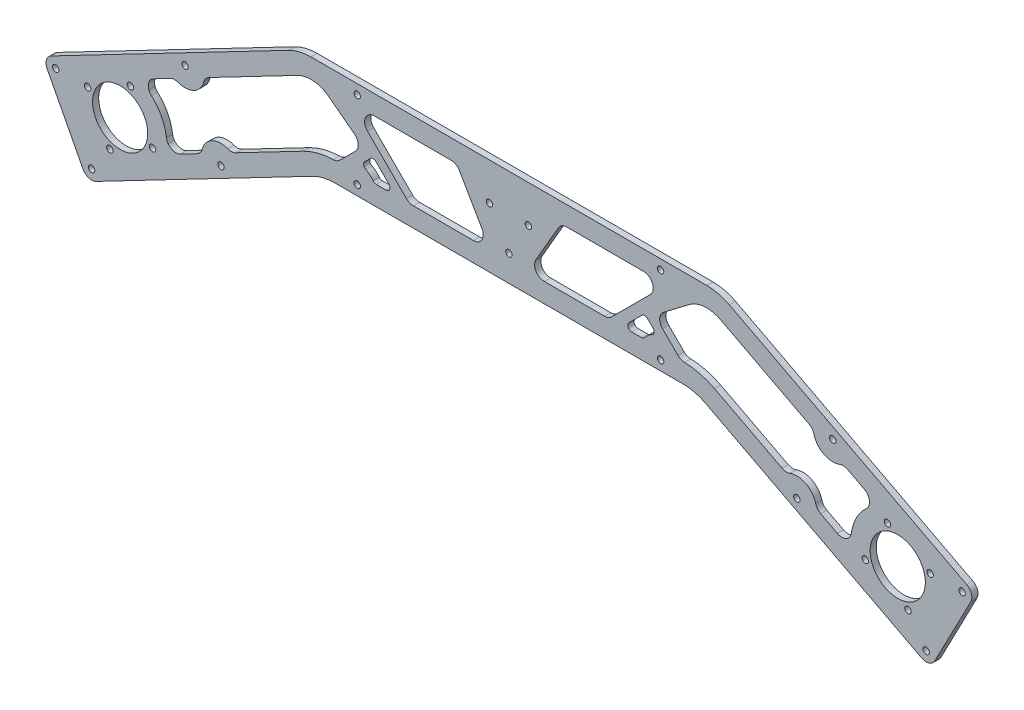
SolidWorks part; units mm, degrees
material "6061-T6 (SS)"
ref_plane "Front Plane" through (0, 0, 0) normal (0, 0, 1) x (1, 0, 0)
ref_plane "Top Plane" through (0, 0, 0) normal (0, 1, 0) x (1, 0, 0)
ref_plane "Right Plane" through (0, 0, 0) normal (1, 0, 0) x (0, 0, -1)
sketch "Sketch1" plane through (0, 0, 0) normal (0, 0, 1) x (1, 0, 0)
  line L0 (-200, -104.1134) -> (0, 0) construction
  line L1 (0, 0) -> (200, -104.1134) construction
  line L2 (-216.69, -98.8511) -> (-194.7376, -87.4234) construction
  line L3 (-113.3558, -30.8247) -> (-235.4371, -94.3763)
  line L4 (-237.5634, -101.1201) -> (-219.0935, -136.6005)
  line L5 (-212.3497, -138.7268) -> (-101.1208, -80.8247)
  line L6 (-101.8121, -28) -> (101.8121, -28)
  line L7 (0, -28) -> (0, -78) construction
  line L8 (89.5771, -78) -> (-89.5771, -78)
  line L9 (113.3558, -30.8247) -> (235.4371, -94.3763)
  line L10 (237.5634, -101.1201) -> (219.0935, -136.6005)
  line L11 (212.3497, -138.7268) -> (101.1208, -80.8247)
  circle A1 centre (-200, -104.1134) radius 14.2
  circle A2 centre (-216.69, -98.8511) radius 1.65
  circle A3 centre (-194.7376, -87.4234) radius 1.65
  circle A4 centre (-183.31, -109.3758) radius 1.65
  circle A5 centre (-205.2624, -120.8035) radius 1.65
  arc A6 (-235.4371, -94.3763) -> (-237.5634, -101.1201) centre (-233.1284, -98.8113) ccw
  arc A7 (-219.0935, -136.6005) -> (-212.3497, -138.7268) centre (-214.6584, -134.2918) ccw
  circle A8 centre (0, 0) radius 25 construction
  circle A11 centre (-200, -104.1134) radius 33.55 construction
  circle A12 centre (205.2624, -120.8035) radius 1.65
  circle A13 centre (216.69, -98.8511) radius 1.65
  circle A14 centre (194.7376, -87.4234) radius 1.65
  circle A15 centre (183.31, -109.3758) radius 1.65
  circle A16 centre (200, -104.1134) radius 14.2
  arc A17 (235.4371, -94.3763) -> (237.5634, -101.1201) centre (233.1284, -98.8113) cw
  arc A18 (219.0935, -136.6005) -> (212.3497, -138.7268) centre (214.6584, -134.2918) cw
  circle A19 centre (-10, -47.2265) radius 1.65
  circle A20 centre (10, -47.2265) radius 1.65
  circle A21 centre (0, -64.547) radius 1.65
  arc A22 (101.1208, -80.8247) -> (89.5771, -78) centre (89.5771, -103) ccw
  arc A23 (113.3558, -30.8247) -> (101.8121, -28) centre (101.8121, -53) ccw
  arc A24 (-113.3558, -30.8247) -> (-101.8121, -28) centre (-101.8121, -53) cw
  arc A25 (-101.1208, -80.8247) -> (-89.5771, -78) centre (-89.5771, -103) cw
  point P17 (-200, -104.1134)
  point P27 (0, -53)
  point P28 (0, -25)
  point P53 (0, -53)
  point P54 (95.6946, -78)
  point P57 (107.9295, -28)
  point P60 (-107.9295, -28)
  point P63 (-95.6946, -78)
  dimension "D1" = 400
  dimension "D3" = 28.4
  dimension "D5" = 3.3
  dimension "D7" = 50
  dimension "D10" = 5
  dimension "D11" = 3.3
  dimension "D12" = 67.1
  dimension "D14" = 3
  dimension "D16" = 25
  dimension "D2" = 125
  dimension "D6" = 35
  dimension "D8" = 3
  dimension "D9" = 50
  dimension "D13" = 50
  dimension "D15" = 20
  dimension "D4" = 4
extrude "Base" add sketch "Sketch1" along normal blind 3.175
sketch "Sketch3" plane through (0, 0, 3.175) normal (0, 0, 1) x (1, 0, 0)
  line L1 (-89.5771, -78) -> (89.5771, -78) construction
  line L2 (-228.3285, -118.8603) -> (-187.4044, -97.5566) construction
  line L3 (101.8121, -28) -> (-101.8121, -28) construction
  line L4 (-237.5634, -101.1201) -> (-219.0935, -136.6005) construction
  line L5 (0, -28) -> (0, -78) construction
  circle A0 centre (-214.6584, -134.2918) radius 1.65
  circle A1 centre (-148.1326, -99.6606) radius 1.65
  circle A2 centre (-78.0312, -73) radius 1.65
  circle A3 centre (-78.0312, -33) radius 1.65
  circle A4 centre (-200, -104.1134) radius 14.2 construction
  circle A5 centre (-166.6026, -64.1802) radius 1.65
  circle A6 centre (-233.1284, -98.8113) radius 1.65
  circle A7 centre (233.1284, -98.8113) radius 1.65
  circle A8 centre (166.6026, -64.1802) radius 1.65
  circle A9 centre (78.0312, -33) radius 1.65
  circle A10 centre (78.0312, -73) radius 1.65
  circle A11 centre (148.1326, -99.6606) radius 1.65
  circle A12 centre (214.6584, -134.2918) radius 1.65
  dimension "D1" = 3.3
  dimension "D3" = 75
  dimension "D6" = 5
  dimension "D4" = 5
  dimension "D5" = 75
  dimension "D2" = 2
extrude "Strut Holes" cut sketch "Sketch3" against normal through all
sketch "Sketch4" plane through (0, 0, 0) normal (0, 0, -1) x (-1, 0, 0)
  line L0 (-168.9602, -104.8658) -> (-160.3585, -100.3881)
  line L1 (-101.1208, -80.8247) -> (-212.3497, -138.7268) construction
  line L2 (-140.5243, -90.063) -> (-105.7383, -71.9546)
  line L3 (-86.9223, -66.5452) -> (-79.0095, -58.6325)
  line L4 (-79.5169, -51.1182) -> (-92.7277, -41.0638)
  line L5 (-182.8126, -78.2555) -> (-174.2109, -73.7777)
  line L6 (-235.4371, -94.3763) -> (-113.3558, -30.8247) construction
  line L7 (-154.3768, -63.4527) -> (-108.7383, -39.6948)
  line L8 (89.5771, -78) -> (-89.5771, -78) construction
  line L9 (-68.2844, -68) -> (-63.1994, -68)
  line L10 (-61.7852, -64.5858) -> (-68.4242, -57.9467)
  line L11 (-71.2527, -57.9467) -> (-74.1321, -60.8262)
  line L12 (-25.4306, -40.5) -> (-13.8835, -60.5)
  line L13 (-18.2137, -68) -> (-49.2288, -68)
  line L14 (-52.7643, -66.5355) -> (-72.7643, -46.5355)
  line L15 (-69.2288, -38) -> (-29.7607, -38)
  line L16 (-101.8121, -28) -> (101.8121, -28) construction
  line L17 (0, -28) -> (0, -78) construction
  line L18 (52.7643, -66.5355) -> (72.7643, -46.5355)
  line L19 (18.2137, -68) -> (49.2288, -68)
  line L20 (25.4306, -40.5) -> (13.8835, -60.5)
  line L21 (69.2288, -38) -> (29.7607, -38)
  line L22 (68.2844, -68) -> (63.1994, -68)
  line L23 (61.7852, -64.5858) -> (68.4242, -57.9467)
  line L24 (71.2527, -57.9467) -> (74.1321, -60.8262)
  line L25 (154.3768, -63.4527) -> (108.7383, -39.6948)
  line L26 (182.8126, -78.2555) -> (174.2109, -73.7777)
  line L27 (168.9602, -104.8658) -> (160.3585, -100.3881)
  line L28 (140.5243, -90.063) -> (105.7383, -71.9546)
  line L29 (86.9223, -66.5452) -> (79.0095, -58.6325)
  line L30 (79.5169, -51.1182) -> (92.7277, -41.0638)
  arc A0 (-183.8835, -86.3298) -> (-176.1884, -101.1118) centre (-200, -104.1134) cw
  circle A1 centre (-183.31, -109.3758) radius 10 construction
  circle A2 centre (-194.7376, -87.4234) radius 10 construction
  arc A3 (-157.8223, -97.1889) -> (-144.5996, -90.3055) centre (-148.1326, -99.6606) cw
  arc A4 (-105.7383, -71.9546) -> (-90.3477, -68.0085) centre (-89.5771, -103) cw
  arc A5 (-89.5771, -78) -> (-101.1208, -80.8247) centre (-89.5771, -103) ccw construction
  arc A6 (-170.1356, -73.5353) -> (-156.9129, -66.6519) centre (-166.6026, -64.1802) ccw
  arc A7 (-108.7383, -39.6948) -> (-92.7277, -41.0638) centre (-101.8121, -53) cw
  arc A8 (-101.8121, -28) -> (-113.3558, -30.8247) centre (-101.8121, -53) ccw construction
  arc A9 (-69.9089, -67.1667) -> (-73.6035, -64.0337) centre (-78.0312, -73) ccw
  circle A10 centre (-10, -47.2265) radius 10 construction
  circle A11 centre (0, -64.547) radius 10 construction
  arc A12 (-156.9129, -66.6519) -> (-154.3768, -63.4527) centre (-152.068, -67.8878) cw
  arc A13 (-174.2109, -73.7777) -> (-170.1356, -73.5353) centre (-171.9022, -78.2128) cw
  arc A14 (-185.2557, -84.2462) -> (-182.8126, -78.2555) centre (-180.5039, -82.6905) cw
  arc A15 (-183.8835, -86.3298) -> (-185.2557, -84.2462) centre (-180.5259, -82.6248) cw
  arc A16 (-176.1884, -101.1118) -> (-175.2688, -103.4309) centre (-171.2277, -100.4865) ccw
  arc A17 (-175.2688, -103.4309) -> (-168.9602, -104.8658) centre (-171.2689, -100.4308) ccw
  arc A18 (-160.3585, -100.3881) -> (-157.8223, -97.1889) centre (-162.6672, -95.953) ccw
  arc A19 (-144.5996, -90.3055) -> (-140.5243, -90.063) centre (-142.833, -85.628) ccw
  arc A20 (-79.0095, -58.6325) -> (-79.5169, -51.1182) centre (-82.545, -55.0969) ccw
  arc A21 (-90.3477, -68.0085) -> (-86.9223, -66.5452) centre (-90.4578, -63.0097) ccw
  arc A22 (-49.2288, -68) -> (-52.7643, -66.5355) centre (-49.2288, -63) cw
  arc A23 (-25.4306, -40.5) -> (-29.7607, -38) centre (-29.7607, -43) ccw
  arc A24 (-13.8835, -60.5) -> (-18.2137, -68) centre (-18.2137, -63) cw
  arc A25 (-72.7643, -46.5355) -> (-69.2288, -38) centre (-69.2288, -43) cw
  arc A26 (-68.4242, -57.9467) -> (-71.2527, -57.9467) centre (-69.8385, -59.3609) ccw
  arc A27 (-68.2844, -68) -> (-69.9089, -67.1667) centre (-68.2844, -66) cw
  arc A28 (-74.1321, -60.8262) -> (-73.6035, -64.0337) centre (-72.7179, -62.2404) ccw
  arc A29 (-63.1994, -68) -> (-61.7852, -64.5858) centre (-63.1994, -66) ccw
  arc A30 (49.2288, -68) -> (52.7643, -66.5355) centre (49.2288, -63) ccw
  arc A31 (13.8835, -60.5) -> (18.2137, -68) centre (18.2137, -63) ccw
  arc A32 (25.4306, -40.5) -> (29.7607, -38) centre (29.7607, -43) cw
  arc A33 (72.7643, -46.5355) -> (69.2288, -38) centre (69.2288, -43) ccw
  arc A34 (63.1994, -68) -> (61.7852, -64.5858) centre (63.1994, -66) cw
  arc A35 (68.4242, -57.9467) -> (71.2527, -57.9467) centre (69.8385, -59.3609) cw
  arc A36 (68.2844, -68) -> (69.9089, -67.1667) centre (68.2844, -66) ccw
  arc A37 (74.1321, -60.8262) -> (73.6035, -64.0337) centre (72.7179, -62.2404) cw
  arc A38 (69.9089, -67.1667) -> (73.6035, -64.0337) centre (78.0312, -73) cw
  arc A39 (156.9129, -66.6519) -> (154.3768, -63.4527) centre (152.068, -67.8878) ccw
  arc A40 (170.1356, -73.5353) -> (156.9129, -66.6519) centre (166.6026, -64.1802) cw
  arc A41 (174.2109, -73.7777) -> (170.1356, -73.5353) centre (171.9022, -78.2128) ccw
  arc A42 (185.2557, -84.2462) -> (182.8126, -78.2555) centre (180.5039, -82.6905) ccw
  circle A43 centre (194.7376, -87.4234) radius 10 construction
  arc A44 (183.8835, -86.3298) -> (185.2557, -84.2462) centre (180.5259, -82.6248) ccw
  arc A45 (183.8835, -86.3298) -> (176.1884, -101.1118) centre (200, -104.1134) ccw
  arc A46 (176.1884, -101.1118) -> (175.2688, -103.4309) centre (171.2277, -100.4865) cw
  circle A47 centre (183.31, -109.3758) radius 10 construction
  arc A48 (175.2688, -103.4309) -> (168.9602, -104.8658) centre (171.2689, -100.4308) cw
  arc A49 (160.3585, -100.3881) -> (157.8223, -97.1889) centre (162.6672, -95.953) cw
  arc A50 (157.8223, -97.1889) -> (144.5996, -90.3055) centre (148.1326, -99.6606) ccw
  arc A51 (144.5996, -90.3055) -> (140.5243, -90.063) centre (142.833, -85.628) cw
  arc A52 (105.7383, -71.9546) -> (90.3477, -68.0085) centre (89.5771, -103) ccw
  arc A53 (90.3477, -68.0085) -> (86.9223, -66.5452) centre (90.4578, -63.0097) cw
  arc A54 (79.0095, -58.6325) -> (79.5169, -51.1182) centre (82.545, -55.0969) cw
  arc A55 (108.7383, -39.6948) -> (92.7277, -41.0638) centre (101.8121, -53) ccw
  point P66 (0, 0)
  point P75 (-74.9619, -54.5849)
  point P78 (-88.3969, -68.0199)
  point P91 (-69.3709, -68)
  point P96 (-58.3709, -68)
  point P132 (0, 0)
  point P142 (0, 0)
  point P166 (0, 0)
  point P167 (0, 0)
  dimension "D1" = 24
  dimension "D2" = 10
  dimension "D4" = 10
  dimension "D5" = 11.5
  dimension "D6" = 5
  dimension "D10" = 2.2457
  dimension "D15" = 5
  dimension "D16" = 5
  dimension "D17" = 2
  dimension "D3" = 10
  dimension "45" = 45
  dimension "D7" = 11.5
  dimension "D8" = 10
  dimension "D9" = 45
  dimension "D11" = 19
  dimension "D12" = 11
  dimension "D13" = 10
  dimension "D14" = 10
extrude "Lightening Holes" cut sketch "Sketch4" against normal through all
